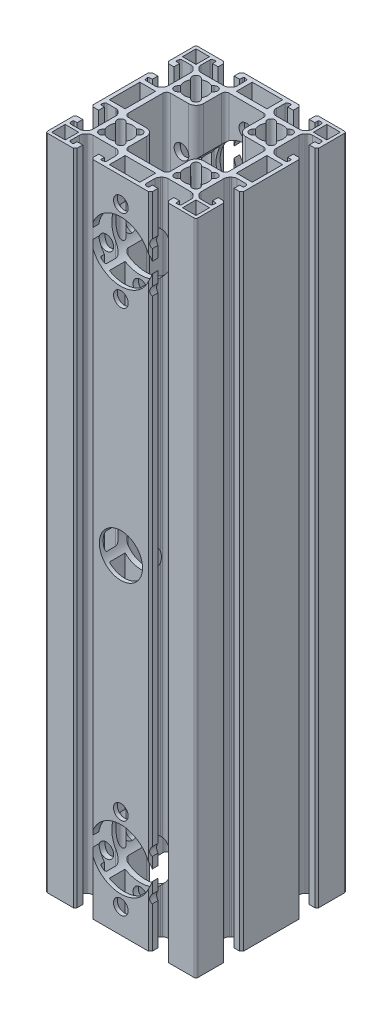
SolidWorks part; units mm, degrees
material "6063-T6"
ref_plane "Front Plane" through (0, 0, 0) normal (0, 0, 1) x (1, 0, 0)
ref_plane "Top Plane" through (0, 0, 0) normal (0, 1, 0) x (1, 0, 0)
ref_plane "Right Plane" through (0, 0, 0) normal (1, 0, 0) x (0, 0, -1)
sketch "Sketch1" plane through (0, 0, 0) normal (0, 1, 0) x (1, 0, 0)
  line L0 (16.5224, 10.1082) -> (17.1083, 10.6941)
  line L2 (14.2799, 13.5226) -> (13.694, 12.9366)
  line L7 (13.694, 19.6541) -> (14.2799, 19.0682)
  line L8 (17.1083, 21.8966) -> (16.5224, 22.4826)
  line L9 (23.2399, 22.4826) -> (22.654, 21.8966)
  line L10 (25.4824, 19.0682) -> (26.0683, 19.6541)
  line L11 (26.0683, 12.9366) -> (25.4824, 13.5226)
  line L12 (22.654, 10.6941) -> (23.2399, 10.1082)
  line L13 (-29.7188, -11.8046) -> (-29.7188, 4.3954)
  line L14 (-38.1188, -11.8046) -> (-29.7188, -11.8046)
  line L15 (-38.1188, 4.3954) -> (-38.1188, -11.8046)
  line L16 (-29.7188, 4.3954) -> (-38.1188, 4.3954)
  line L17 (-23.4776, 10.1082) -> (-22.8917, 10.6941)
  line L18 (-25.7201, 13.5226) -> (-26.306, 12.9366)
  line L19 (-26.306, 19.6541) -> (-25.7201, 19.0682)
  line L20 (-22.8917, 21.8966) -> (-23.4776, 22.4826)
  line L21 (-16.7601, 22.4826) -> (-17.346, 21.8966)
  line L22 (-14.5176, 19.0682) -> (-13.9317, 19.6541)
  line L23 (-13.9317, 12.9366) -> (-14.5176, 13.5226)
  line L24 (-17.346, 10.6941) -> (-16.7601, 10.1082)
  line L26 (23.2399, -17.5174) -> (22.654, -18.1034)
  line L27 (25.4824, -20.9318) -> (26.0683, -20.3459)
  line L28 (26.0683, -27.0634) -> (25.4824, -26.4774)
  line L29 (22.654, -29.3059) -> (23.2399, -29.8918)
  line L30 (16.5224, -29.8918) -> (17.1083, -29.3059)
  line L31 (14.2799, -26.4774) -> (13.694, -27.0634)
  line L32 (13.694, -20.3459) -> (14.2799, -20.9318)
  line L33 (17.1083, -18.1034) -> (16.5224, -17.5174)
  line L41 (-31.3188, -34.9046) -> (-38.5188, -34.9046)
  line L42 (-31.3188, -42.1046) -> (-31.3188, -34.9046)
  line L43 (-38.5188, -42.1046) -> (-31.3188, -42.1046)
  line L44 (-38.5188, -34.9046) -> (-38.5188, -42.1046)
  line L45 (-16.7601, -17.5174) -> (-17.346, -18.1034)
  line L46 (-14.5176, -20.9318) -> (-13.9317, -20.3459)
  line L51 (-13.9317, -27.0634) -> (-14.5176, -26.4774)
  line L52 (-17.346, -29.3059) -> (-16.7601, -29.8918)
  line L53 (-23.4776, -29.8918) -> (-22.8917, -29.3059)
  line L54 (-25.7201, -26.4774) -> (-26.306, -27.0634)
  line L55 (-26.306, -20.3459) -> (-25.7201, -20.9318)
  line L56 (-22.8917, -18.1034) -> (-23.4776, -17.5174)
  line L57 (-38.5188, 27.4954) -> (-31.3188, 27.4954)
  line L58 (-38.5188, 34.6954) -> (-38.5188, 27.4954)
  line L59 (-31.3188, 34.6954) -> (-38.5188, 34.6954)
  line L60 (-31.3188, 27.4954) -> (-31.3188, 34.6954)
  line L61 (38.2812, -34.9046) -> (31.0812, -34.9046)
  line L62 (38.2812, -42.1046) -> (38.2812, -34.9046)
  line L63 (31.0812, -42.1046) -> (38.2812, -42.1046)
  line L64 (31.0812, -34.9046) -> (31.0812, -42.1046)
  line L65 (31.0812, 27.4954) -> (38.2812, 27.4954)
  line L66 (31.0812, 34.6954) -> (31.0812, 27.4954)
  line L67 (38.2812, 34.6954) -> (31.0812, 34.6954)
  line L68 (38.2812, 27.4954) -> (38.2812, 34.6954)
  line L69 (-8.2188, 34.2954) -> (-8.2188, 25.8954)
  line L70 (7.9812, 34.2954) -> (-8.2188, 34.2954)
  line L71 (7.9812, 25.8954) -> (7.9812, 34.2954)
  line L72 (-8.2188, 25.8954) -> (7.9812, 25.8954)
  line L79 (11.0812, -28.5046) -> (11.0812, -18.9046)
  line L80 (-9.3188, -30.5046) -> (9.0812, -30.5046)
  line L81 (-11.3188, -18.9046) -> (-11.3188, -28.5046)
  line L82 (-24.9188, -14.9046) -> (-15.3188, -14.9046)
  line L83 (-26.9188, 5.4954) -> (-26.9188, -12.9046)
  line L84 (-15.3188, 7.4954) -> (-24.9188, 7.4954)
  line L89 (-11.3188, 21.0954) -> (-11.3188, 11.4954)
  line L90 (9.0812, 23.0954) -> (-9.3188, 23.0954)
  line L91 (11.0812, 11.4954) -> (11.0812, 21.0954)
  line L92 (24.6812, 7.4954) -> (15.0812, 7.4954)
  line L93 (26.6812, -12.9046) -> (26.6812, 5.4954)
  line L94 (15.0812, -14.9046) -> (24.6812, -14.9046)
  line L95 (7.9812, -33.3046) -> (-8.2188, -33.3046)
  line L96 (7.9812, -41.7046) -> (7.9812, -33.3046)
  line L97 (-8.2188, -41.7046) -> (7.9812, -41.7046)
  line L98 (-8.2188, -33.3046) -> (-8.2188, -41.7046)
  line L99 (29.4812, 4.3954) -> (29.4812, -11.8046)
  line L100 (37.8812, 4.3954) -> (29.4812, 4.3954)
  line L101 (37.8812, -11.8046) -> (37.8812, 4.3954)
  line L102 (29.4812, -11.8046) -> (37.8812, -11.8046)
  line L103 (39.8812, -42.7046) -> (39.8812, -28.9546)
  line L104 (39.8812, -28.9546) -> (38.8812, -27.9546)
  line L105 (38.8812, -27.9546) -> (35.8812, -27.9546)
  line L106 (35.8812, -27.9546) -> (35.8812, -30.9546)
  line L107 (35.8812, -30.9546) -> (37.4853, -30.9546)
  line L108 (37.9777, -31.5414) -> (37.7979, -32.5609)
  line L109 (36.9116, -33.3046) -> (32.215, -33.3046)
  line L110 (30.0937, -32.4259) -> (29.5598, -31.8921)
  line L111 (28.6812, -29.7708) -> (28.6812, -17.6385)
  line L118 (29.5598, -15.5172) -> (30.0937, -14.9833)
  line L119 (32.215, -14.1046) -> (36.9116, -14.1046)
  line L120 (37.7979, -14.8483) -> (37.9777, -15.8678)
  line L121 (37.4853, -16.4546) -> (35.8812, -16.4546)
  line L122 (35.8812, -16.4546) -> (35.8812, -19.4546)
  line L123 (35.8812, -19.4546) -> (38.8812, -19.4546)
  line L128 (38.8812, -19.4546) -> (39.8812, -18.4546)
  line L129 (39.8812, -18.4546) -> (39.8812, 11.0454)
  line L130 (39.8812, 11.0454) -> (38.8812, 12.0454)
  line L131 (38.8812, 12.0454) -> (35.8812, 12.0454)
  line L132 (35.8812, 12.0454) -> (35.8812, 9.0454)
  line L133 (35.8812, 9.0454) -> (37.4853, 9.0454)
  line L134 (37.9777, 8.4586) -> (37.7979, 7.4391)
  line L135 (36.9116, 6.6954) -> (32.215, 6.6954)
  line L136 (30.0937, 7.5741) -> (29.5598, 8.1079)
  line L137 (28.6812, 10.2292) -> (28.6812, 22.3615)
  line L138 (29.5598, 24.4828) -> (30.0937, 25.0167)
  line L139 (32.215, 25.8954) -> (36.9116, 25.8954)
  line L140 (37.7979, 25.1517) -> (37.9777, 24.1322)
  line L141 (37.4853, 23.5454) -> (35.8812, 23.5454)
  line L142 (35.8812, 23.5454) -> (35.8812, 20.5454)
  line L143 (35.8812, 20.5454) -> (38.8812, 20.5454)
  line L144 (38.8812, 20.5454) -> (39.8812, 21.5454)
  line L145 (39.8812, 21.5454) -> (39.8812, 35.2954)
  line L146 (38.8812, 36.2954) -> (25.1312, 36.2954)
  line L147 (25.1312, 36.2954) -> (24.1312, 35.2954)
  line L148 (24.1312, 35.2954) -> (24.1312, 32.2954)
  line L149 (24.1312, 32.2954) -> (27.1312, 32.2954)
  line L150 (27.1312, 32.2954) -> (27.1312, 33.8995)
  line L157 (27.718, 34.3919) -> (28.7374, 34.2122)
  line L158 (29.4812, 33.3258) -> (29.4812, 28.6292)
  line L159 (28.6025, 26.5079) -> (28.0686, 25.9741)
  line L160 (25.9473, 25.0954) -> (13.815, 25.0954)
  line L161 (11.6937, 25.9741) -> (11.1598, 26.5079)
  line L162 (10.2812, 28.6292) -> (10.2812, 33.3258)
  line L167 (11.0249, 34.2122) -> (12.0443, 34.3919)
  line L172 (12.6312, 33.8995) -> (12.6312, 32.2954)
  line L173 (12.6312, 32.2954) -> (15.6312, 32.2954)
  line L178 (15.6312, 32.2954) -> (15.6312, 35.2954)
  line L179 (15.6312, 35.2954) -> (14.6312, 36.2954)
  line L183 (14.6312, 36.2954) -> (-14.8688, 36.2954)
  line L184 (-14.8688, 36.2954) -> (-15.8688, 35.2954)
  line L189 (-15.8688, 35.2954) -> (-15.8688, 32.2954)
  line L190 (-15.8688, 32.2954) -> (-12.8688, 32.2954)
  line L195 (-12.8688, 32.2954) -> (-12.8688, 33.8995)
  line L196 (-12.282, 34.3919) -> (-11.2626, 34.2122)
  line L198 (-10.5188, 33.3258) -> (-10.5188, 28.6292)
  line L199 (-11.3975, 26.5079) -> (-11.9314, 25.9741)
  line L200 (-14.0527, 25.0954) -> (-26.185, 25.0954)
  line L201 (-28.3063, 25.9741) -> (-28.8402, 26.5079)
  line L202 (-29.7188, 28.6292) -> (-29.7188, 33.3258)
  line L203 (-28.9751, 34.2122) -> (-27.9557, 34.3919)
  line L204 (-27.3688, 33.8995) -> (-27.3688, 32.2954)
  line L205 (-27.3688, 32.2954) -> (-24.3688, 32.2954)
  line L206 (-24.3688, 32.2954) -> (-24.3688, 35.2954)
  line L207 (-24.3688, 35.2954) -> (-25.3688, 36.2954)
  line L208 (-25.3688, 36.2954) -> (-39.1188, 36.2954)
  line L209 (-40.1188, 35.2954) -> (-40.1188, 21.5454)
  line L210 (-40.1188, 21.5454) -> (-39.1188, 20.5454)
  line L211 (-39.1188, 20.5454) -> (-36.1188, 20.5454)
  line L212 (-36.1188, 20.5454) -> (-36.1188, 23.5454)
  line L213 (-36.1188, 23.5454) -> (-37.723, 23.5454)
  line L214 (-38.2154, 24.1322) -> (-38.0356, 25.1517)
  line L215 (-37.1493, 25.8954) -> (-32.4527, 25.8954)
  line L216 (-30.3314, 25.0167) -> (-29.7975, 24.4828)
  line L217 (-28.9188, 22.3615) -> (-28.9188, 10.2292)
  line L218 (-29.7975, 8.1079) -> (-30.3314, 7.5741)
  line L219 (-32.4527, 6.6954) -> (-37.1493, 6.6954)
  line L220 (-38.0356, 7.4391) -> (-38.2154, 8.4586)
  line L221 (-37.723, 9.0454) -> (-36.1188, 9.0454)
  line L222 (-36.1188, 9.0454) -> (-36.1188, 12.0454)
  line L223 (-36.1188, 12.0454) -> (-39.1188, 12.0454)
  line L224 (-39.1188, 12.0454) -> (-40.1188, 11.0454)
  line L225 (-40.1188, 11.0454) -> (-40.1188, -18.4546)
  line L226 (-40.1188, -18.4546) -> (-39.1188, -19.4546)
  line L227 (-39.1188, -19.4546) -> (-36.1188, -19.4546)
  line L228 (-36.1188, -19.4546) -> (-36.1188, -16.4546)
  line L229 (-36.1188, -16.4546) -> (-37.723, -16.4546)
  line L230 (-38.2154, -15.8678) -> (-38.0356, -14.8483)
  line L231 (-37.1493, -14.1046) -> (-32.4527, -14.1046)
  line L232 (-30.3314, -14.9833) -> (-29.7975, -15.5172)
  line L233 (-28.9188, -17.6385) -> (-28.9188, -29.7708)
  line L234 (-29.7975, -31.8921) -> (-30.3314, -32.4259)
  line L235 (-32.4527, -33.3046) -> (-37.1493, -33.3046)
  line L236 (-38.0356, -32.5609) -> (-38.2154, -31.5414)
  line L237 (-37.723, -30.9546) -> (-36.1188, -30.9546)
  line L238 (-36.1188, -30.9546) -> (-36.1188, -27.9546)
  line L239 (-36.1188, -27.9546) -> (-39.1188, -27.9546)
  line L240 (-39.1188, -27.9546) -> (-40.1188, -28.9546)
  line L241 (-40.1188, -28.9546) -> (-40.1188, -42.7046)
  line L242 (-39.1188, -43.7046) -> (-25.3688, -43.7046)
  line L243 (-25.3688, -43.7046) -> (-24.3688, -42.7046)
  line L244 (-24.3688, -42.7046) -> (-24.3688, -39.7046)
  line L245 (-24.3688, -39.7046) -> (-27.3688, -39.7046)
  line L246 (-27.3688, -39.7046) -> (-27.3688, -41.3087)
  line L247 (-27.9557, -41.8011) -> (-28.9751, -41.6214)
  line L248 (-29.7188, -40.7351) -> (-29.7188, -36.0385)
  line L249 (-28.8402, -33.9172) -> (-28.3063, -33.3833)
  line L250 (-26.185, -32.5046) -> (-14.0527, -32.5046)
  line L251 (-11.9314, -33.3833) -> (-11.3975, -33.9172)
  line L252 (-10.5188, -36.0385) -> (-10.5188, -40.7351)
  line L253 (-11.2626, -41.6214) -> (-12.282, -41.8011)
  line L254 (-12.8688, -41.3087) -> (-12.8688, -39.7046)
  line L255 (-12.8688, -39.7046) -> (-15.8688, -39.7046)
  line L256 (-15.8688, -39.7046) -> (-15.8688, -42.7046)
  line L257 (-15.8688, -42.7046) -> (-14.8688, -43.7046)
  line L258 (-14.8688, -43.7046) -> (14.6312, -43.7046)
  line L259 (14.6312, -43.7046) -> (15.6312, -42.7046)
  line L260 (15.6312, -42.7046) -> (15.6312, -39.7046)
  line L261 (15.6312, -39.7046) -> (12.6312, -39.7046)
  line L262 (12.6312, -39.7046) -> (12.6312, -41.3087)
  line L263 (12.0443, -41.8011) -> (11.0249, -41.6214)
  line L264 (10.2812, -40.7351) -> (10.2812, -36.0385)
  line L265 (11.1598, -33.9172) -> (11.6937, -33.3833)
  line L266 (13.815, -32.5046) -> (25.9473, -32.5046)
  line L267 (28.0686, -33.3833) -> (28.6025, -33.9172)
  line L268 (29.4812, -36.0385) -> (29.4812, -40.7351)
  line L269 (28.7374, -41.6214) -> (27.718, -41.8011)
  line L270 (27.1312, -41.3087) -> (27.1312, -39.7046)
  line L271 (27.1312, -39.7046) -> (24.1312, -39.7046)
  line L272 (24.1312, -39.7046) -> (24.1312, -42.7046)
  line L273 (24.1312, -42.7046) -> (25.1312, -43.7046)
  line L274 (25.1312, -43.7046) -> (38.8812, -43.7046)
  arc A0 (17.1083, 10.6941) -> (22.654, 10.6941) centre (19.8812, 16.2954) ccw
  arc A1 (13.694, 12.9366) -> (16.5224, 10.1082) centre (15.1082, 11.5224) ccw
  arc A2 (14.2799, 19.0682) -> (14.2799, 13.5226) centre (19.8812, 16.2954) ccw
  arc A3 (16.5224, 22.4826) -> (13.694, 19.6541) centre (15.1082, 21.0684) ccw
  arc A4 (22.654, 21.8966) -> (17.1083, 21.8966) centre (19.8812, 16.2954) ccw
  arc A5 (26.0683, 19.6541) -> (23.2399, 22.4826) centre (24.6541, 21.0684) ccw
  arc A6 (25.4824, 13.5226) -> (25.4824, 19.0682) centre (19.8812, 16.2954) ccw
  arc A7 (23.2399, 10.1082) -> (26.0683, 12.9366) centre (24.6541, 11.5224) ccw
  arc A8 (-22.8917, 10.6941) -> (-17.346, 10.6941) centre (-20.1188, 16.2954) ccw
  arc A9 (-26.306, 12.9366) -> (-23.4776, 10.1082) centre (-24.8918, 11.5224) ccw
  arc A10 (-25.7201, 19.0682) -> (-25.7201, 13.5226) centre (-20.1188, 16.2954) ccw
  arc A11 (-23.4776, 22.4826) -> (-26.306, 19.6541) centre (-24.8918, 21.0684) ccw
  arc A12 (-17.346, 21.8966) -> (-22.8917, 21.8966) centre (-20.1188, 16.2954) ccw
  arc A13 (-13.9317, 19.6541) -> (-16.7601, 22.4826) centre (-15.3459, 21.0684) ccw
  arc A14 (-14.5176, 13.5226) -> (-14.5176, 19.0682) centre (-20.1188, 16.2954) ccw
  arc A15 (-16.7601, 10.1082) -> (-13.9317, 12.9366) centre (-15.3459, 11.5224) ccw
  arc A50 (22.654, -18.1034) -> (17.1083, -18.1034) centre (19.8812, -23.7046) ccw
  arc A51 (26.0683, -20.3459) -> (23.2399, -17.5174) centre (24.6541, -18.9316) ccw
  arc A52 (25.4824, -26.4774) -> (25.4824, -20.9318) centre (19.8812, -23.7046) ccw
  arc A53 (23.2399, -29.8918) -> (26.0683, -27.0634) centre (24.6541, -28.4776) ccw
  arc A54 (17.1083, -29.3059) -> (22.654, -29.3059) centre (19.8812, -23.7046) ccw
  arc A55 (13.694, -27.0634) -> (16.5224, -29.8918) centre (15.1082, -28.4776) ccw
  arc A56 (14.2799, -20.9318) -> (14.2799, -26.4774) centre (19.8812, -23.7046) ccw
  arc A57 (16.5224, -17.5174) -> (13.694, -20.3459) centre (15.1082, -18.9316) ccw
  arc A58 (-17.346, -18.1034) -> (-22.8917, -18.1034) centre (-20.1188, -23.7046) ccw
  arc A59 (-13.9317, -20.3459) -> (-16.7601, -17.5174) centre (-15.3459, -18.9316) ccw
  arc A60 (-14.5176, -26.4774) -> (-14.5176, -20.9318) centre (-20.1188, -23.7046) ccw
  arc A61 (-16.7601, -29.8918) -> (-13.9317, -27.0634) centre (-15.3459, -28.4776) ccw
  arc A62 (-22.8917, -29.3059) -> (-17.346, -29.3059) centre (-20.1188, -23.7046) ccw
  arc A63 (-26.306, -27.0634) -> (-23.4776, -29.8918) centre (-24.8918, -28.4776) ccw
  arc A64 (-25.7201, -20.9318) -> (-25.7201, -26.4774) centre (-20.1188, -23.7046) ccw
  arc A65 (-23.4776, -17.5174) -> (-26.306, -20.3459) centre (-24.8918, -18.9316) ccw
  arc A66 (15.0812, -14.9046) -> (11.0812, -18.9046) centre (15.0812, -18.9046) ccw
  arc A67 (9.0812, -30.5046) -> (11.0812, -28.5046) centre (9.0812, -28.5046) ccw
  arc A68 (-11.3188, -28.5046) -> (-9.3188, -30.5046) centre (-9.3188, -28.5046) ccw
  arc A69 (-11.3188, -18.9046) -> (-15.3188, -14.9046) centre (-15.3188, -18.9046) ccw
  arc A70 (-26.9188, -12.9046) -> (-24.9188, -14.9046) centre (-24.9188, -12.9046) ccw
  arc A71 (-24.9188, 7.4954) -> (-26.9188, 5.4954) centre (-24.9188, 5.4954) ccw
  arc A72 (-15.3188, 7.4954) -> (-11.3188, 11.4954) centre (-15.3188, 11.4954) ccw
  arc A73 (-9.3188, 23.0954) -> (-11.3188, 21.0954) centre (-9.3188, 21.0954) ccw
  arc A74 (11.0812, 21.0954) -> (9.0812, 23.0954) centre (9.0812, 21.0954) ccw
  arc A75 (11.0812, 11.4954) -> (15.0812, 7.4954) centre (15.0812, 11.4954) ccw
  arc A76 (26.6812, 5.4954) -> (24.6812, 7.4954) centre (24.6812, 5.4954) ccw
  arc A77 (24.6812, -14.9046) -> (26.6812, -12.9046) centre (24.6812, -12.9046) ccw
  arc A78 (38.8812, -43.7046) -> (39.8812, -42.7046) centre (38.8812, -42.7046) ccw
  arc A79 (37.9777, -31.5414) -> (37.4853, -30.9546) centre (37.4853, -31.4546) ccw
  arc A80 (36.9116, -33.3046) -> (37.7979, -32.5609) centre (36.9116, -32.4046) ccw
  arc A81 (30.0937, -32.4259) -> (32.215, -33.3046) centre (32.215, -30.3046) ccw
  arc A82 (28.6812, -29.7708) -> (29.5598, -31.8921) centre (31.6812, -29.7708) ccw
  arc A83 (29.5598, -15.5172) -> (28.6812, -17.6385) centre (31.6812, -17.6385) ccw
  arc A84 (32.215, -14.1046) -> (30.0937, -14.9833) centre (32.215, -17.1046) ccw
  arc A85 (37.7979, -14.8483) -> (36.9116, -14.1046) centre (36.9116, -15.0046) ccw
  arc A86 (37.4853, -16.4546) -> (37.9777, -15.8678) centre (37.4853, -15.9546) ccw
  arc A87 (37.9777, 8.4586) -> (37.4853, 9.0454) centre (37.4853, 8.5454) ccw
  arc A88 (36.9116, 6.6954) -> (37.7979, 7.4391) centre (36.9116, 7.5954) ccw
  arc A89 (30.0937, 7.5741) -> (32.215, 6.6954) centre (32.215, 9.6954) ccw
  arc A90 (28.6812, 10.2292) -> (29.5598, 8.1079) centre (31.6812, 10.2292) ccw
  arc A91 (29.5598, 24.4828) -> (28.6812, 22.3615) centre (31.6812, 22.3615) ccw
  arc A92 (32.215, 25.8954) -> (30.0937, 25.0167) centre (32.215, 22.8954) ccw
  arc A93 (37.7979, 25.1517) -> (36.9116, 25.8954) centre (36.9116, 24.9954) ccw
  arc A94 (37.4853, 23.5454) -> (37.9777, 24.1322) centre (37.4853, 24.0454) ccw
  arc A95 (39.8812, 35.2954) -> (38.8812, 36.2954) centre (38.8812, 35.2954) ccw
  arc A96 (27.718, 34.3919) -> (27.1312, 33.8995) centre (27.6312, 33.8995) ccw
  arc A97 (29.4812, 33.3258) -> (28.7374, 34.2122) centre (28.5812, 33.3258) ccw
  arc A98 (28.6025, 26.5079) -> (29.4812, 28.6292) centre (26.4812, 28.6292) ccw
  arc A99 (25.9473, 25.0954) -> (28.0686, 25.9741) centre (25.9473, 28.0954) ccw
  arc A100 (11.6937, 25.9741) -> (13.815, 25.0954) centre (13.815, 28.0954) ccw
  arc A101 (10.2812, 28.6292) -> (11.1598, 26.5079) centre (13.2812, 28.6292) ccw
  arc A102 (11.0249, 34.2122) -> (10.2812, 33.3258) centre (11.1812, 33.3258) ccw
  arc A103 (12.6312, 33.8995) -> (12.0443, 34.3919) centre (12.1312, 33.8995) ccw
  arc A104 (-12.282, 34.3919) -> (-12.8688, 33.8995) centre (-12.3688, 33.8995) ccw
  arc A105 (-10.5188, 33.3258) -> (-11.2626, 34.2122) centre (-11.4188, 33.3258) ccw
  arc A106 (-11.3975, 26.5079) -> (-10.5188, 28.6292) centre (-13.5188, 28.6292) ccw
  arc A107 (-14.0527, 25.0954) -> (-11.9314, 25.9741) centre (-14.0527, 28.0954) ccw
  arc A108 (-28.3063, 25.9741) -> (-26.185, 25.0954) centre (-26.185, 28.0954) ccw
  arc A109 (-29.7188, 28.6292) -> (-28.8402, 26.5079) centre (-26.7188, 28.6292) ccw
  arc A110 (-28.9751, 34.2122) -> (-29.7188, 33.3258) centre (-28.8188, 33.3258) ccw
  arc A111 (-27.3688, 33.8995) -> (-27.9557, 34.3919) centre (-27.8688, 33.8995) ccw
  arc A112 (-39.1188, 36.2954) -> (-40.1188, 35.2954) centre (-39.1188, 35.2954) ccw
  arc A113 (-38.2154, 24.1322) -> (-37.723, 23.5454) centre (-37.723, 24.0454) ccw
  arc A114 (-37.1493, 25.8954) -> (-38.0356, 25.1517) centre (-37.1493, 24.9954) ccw
  arc A115 (-30.3314, 25.0167) -> (-32.4527, 25.8954) centre (-32.4527, 22.8954) ccw
  arc A116 (-28.9188, 22.3615) -> (-29.7975, 24.4828) centre (-31.9188, 22.3615) ccw
  arc A117 (-29.7975, 8.1079) -> (-28.9188, 10.2292) centre (-31.9188, 10.2292) ccw
  arc A118 (-32.4527, 6.6954) -> (-30.3314, 7.5741) centre (-32.4527, 9.6954) ccw
  arc A119 (-38.0356, 7.4391) -> (-37.1493, 6.6954) centre (-37.1493, 7.5954) ccw
  arc A120 (-37.723, 9.0454) -> (-38.2154, 8.4586) centre (-37.723, 8.5454) ccw
  arc A121 (-38.2154, -15.8678) -> (-37.723, -16.4546) centre (-37.723, -15.9546) ccw
  arc A122 (-37.1493, -14.1046) -> (-38.0356, -14.8483) centre (-37.1493, -15.0046) ccw
  arc A123 (-30.3314, -14.9833) -> (-32.4527, -14.1046) centre (-32.4527, -17.1046) ccw
  arc A124 (-28.9188, -17.6385) -> (-29.7975, -15.5172) centre (-31.9188, -17.6385) ccw
  arc A125 (-29.7975, -31.8921) -> (-28.9188, -29.7708) centre (-31.9188, -29.7708) ccw
  arc A126 (-32.4527, -33.3046) -> (-30.3314, -32.4259) centre (-32.4527, -30.3046) ccw
  arc A127 (-38.0356, -32.5609) -> (-37.1493, -33.3046) centre (-37.1493, -32.4046) ccw
  arc A128 (-37.723, -30.9546) -> (-38.2154, -31.5414) centre (-37.723, -31.4546) ccw
  arc A129 (-40.1188, -42.7046) -> (-39.1188, -43.7046) centre (-39.1188, -42.7046) ccw
  arc A130 (-27.9557, -41.8011) -> (-27.3688, -41.3087) centre (-27.8688, -41.3087) ccw
  arc A131 (-29.7188, -40.7351) -> (-28.9751, -41.6214) centre (-28.8188, -40.7351) ccw
  arc A132 (-28.8402, -33.9172) -> (-29.7188, -36.0385) centre (-26.7188, -36.0385) ccw
  arc A133 (-26.185, -32.5046) -> (-28.3063, -33.3833) centre (-26.185, -35.5046) ccw
  arc A134 (-11.9314, -33.3833) -> (-14.0527, -32.5046) centre (-14.0527, -35.5046) ccw
  arc A135 (-10.5188, -36.0385) -> (-11.3975, -33.9172) centre (-13.5188, -36.0385) ccw
  arc A136 (-11.2626, -41.6214) -> (-10.5188, -40.7351) centre (-11.4188, -40.7351) ccw
  arc A137 (-12.8688, -41.3087) -> (-12.282, -41.8011) centre (-12.3688, -41.3087) ccw
  arc A138 (12.0443, -41.8011) -> (12.6312, -41.3087) centre (12.1312, -41.3087) ccw
  arc A139 (10.2812, -40.7351) -> (11.0249, -41.6214) centre (11.1812, -40.7351) ccw
  arc A140 (11.1598, -33.9172) -> (10.2812, -36.0385) centre (13.2812, -36.0385) ccw
  arc A141 (13.815, -32.5046) -> (11.6937, -33.3833) centre (13.815, -35.5046) ccw
  arc A142 (28.0686, -33.3833) -> (25.9473, -32.5046) centre (25.9473, -35.5046) ccw
  arc A143 (29.4812, -36.0385) -> (28.6025, -33.9172) centre (26.4812, -36.0385) ccw
  arc A144 (28.7374, -41.6214) -> (29.4812, -40.7351) centre (28.5812, -40.7351) ccw
  arc A145 (27.1312, -41.3087) -> (27.718, -41.8011) centre (27.6312, -41.3087) ccw
extrude "Boss-Extrude1" add sketch "Sketch1" along normal blind 350
sketch "Sketch2" plane through (0, 0, 43.7046) normal (0, 0, 1) x (1, 0, 0)
  line L0 (-0.1188, 350) -> (0, 0) construction
  line L1 (-14.8688, 350) -> (14.6312, 350) construction
  line L2 (-39.1188, 175) -> (39.8812, 175) construction
  line L3 (-39.1188, 350) -> (-39.1188, 0) construction
  line L4 (39.8812, 350) -> (39.8812, 0) construction
  line L5 (25.1312, 203.5189) -> (14.6312, 203.5189) construction
  line L6 (25.1312, 350) -> (25.1312, 0) construction
  line L7 (14.6312, 350) -> (14.6312, 0) construction
  circle A0 centre (-0.0594, 175) radius 11.5
  circle A1 centre (-0.107, 315) radius 17.5 construction
  circle A2 centre (-0.107, 35) radius 17.5 construction
  circle A3 centre (-0.107, 315) radius 16
  circle A4 centre (-0.107, 293.13) radius 3.9
  circle A5 centre (-19.0469, 304.065) radius 3.9
  circle A6 centre (-19.0469, 325.935) radius 3.9
  circle A7 centre (-0.107, 336.87) radius 3.9
  circle A8 centre (18.833, 325.935) radius 3.9
  circle A9 centre (18.833, 304.065) radius 3.9
  circle A10 centre (18.833, 45.935) radius 3.9
  circle A11 centre (18.833, 24.065) radius 3.9
  circle A12 centre (-0.107, 13.13) radius 3.9
  circle A13 centre (-19.0469, 24.065) radius 3.9
  circle A14 centre (-19.0469, 45.935) radius 3.9
  circle A15 centre (-0.107, 56.87) radius 3.9
  circle A16 centre (-0.107, 35) radius 16
  circle A17 centre (19.8812, 203.5189) radius 4
  circle A18 centre (-20.0194, 203.5053) radius 4
  circle A19 centre (19.8812, 146.4811) radius 4
  circle A20 centre (-20.0194, 146.4947) radius 4
  point P31 (-0.107, 315)
  dimension "D1" = 23
  dimension "D2" = 35
  dimension "D4" = 8
  dimension "D5" = 7.8
  dimension "D3" = 35
extrude "Cut-Extrude1" cut sketch "Sketch2" against normal through all
sketch "Sketch4" plane through (0, 0, -36.2954) normal (0, 0, -1) x (-1, 0, 0)
  line L0 (-39.8812, 175) -> (39.1188, 175) construction
  line L1 (-39.8812, 350) -> (-39.8812, 0) construction
  line L2 (39.1188, 350) -> (39.1188, 0) construction
  line L3 (-49.4482, 280) -> (87.1789, 280)
  line L5 (-49.4482, 70) -> (87.1789, 70)
  dimension "D1" = 105
split line "Split Line2"
